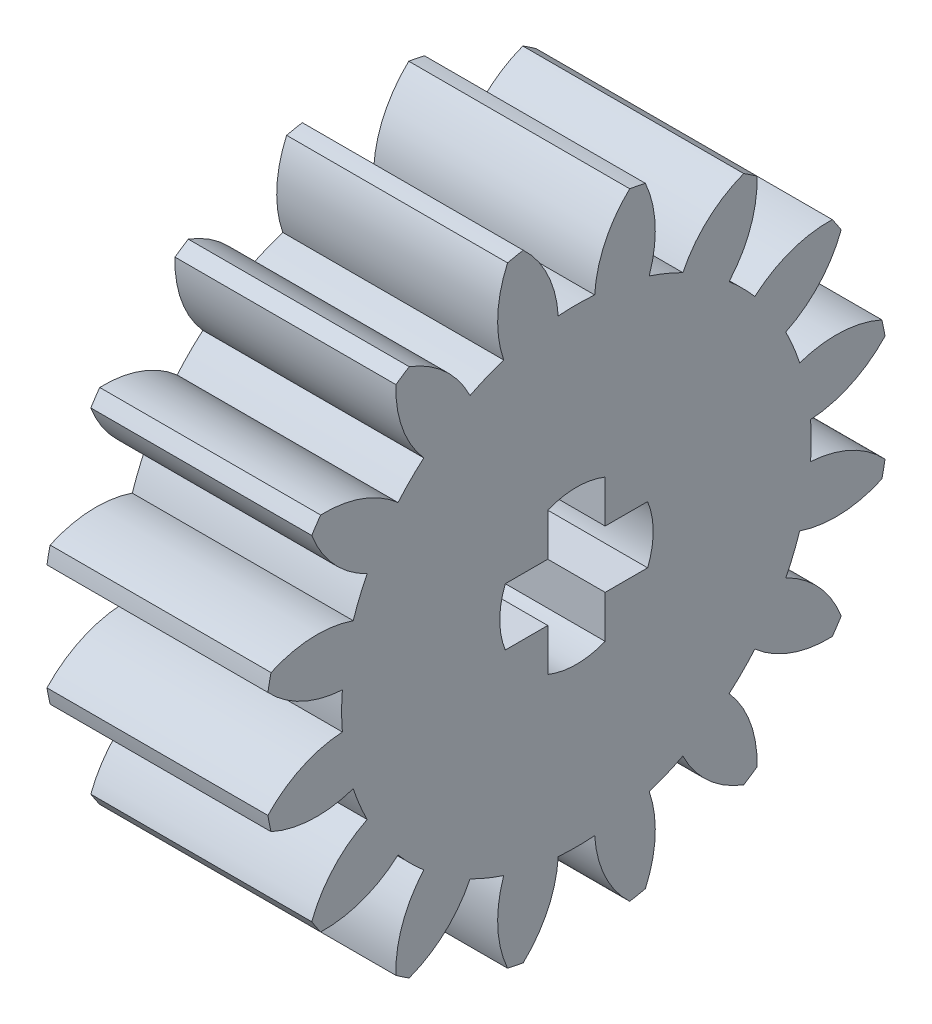
SolidWorks part; units mm, degrees
ref_plane "Plane1" through (0, 0, 0) normal (0, 0, 1) x (1, 0, 0)
ref_plane "Plane2" through (0, 0, 0) normal (0, 1, 0) x (1, 0, 0)
ref_plane "Plane3" through (0, 0, 0) normal (1, 0, 0) x (0, 0, -1)
sketch "HoldingSke" plane through (0, 0, 0) normal (0, 1, 0) x (1, 0, 0)
  line L0 (0, 0) -> (0.9613, -0.2756)
  line L1 (-15, 0) -> (100, 0) construction
  line L2 (0, 0) -> (-2.1039, 2.3779)
  line L3 (0, 0) -> (-11.863, 4.5341)
  line L4 (0, 0) -> (8.3015, 2.3804)
  line L5 (0, 0) -> (-46.8476, -17.4728)
  line L6 (0, 0) -> (-5.2639, -3.5516)
  line L7 (-2.1039, 2.3779) -> (8.6586, 51.2059)
  line L8 (-76.2, 54.61) -> (-76.1, 54.61)
  line L9 (-71.009, 38.7566) -> (-53.1078, 45.2721)
  line L10 (-76.2, 71.12) -> (104.1128, 71.12)
  line L11 (0, 0) -> (-6.35, 0)
  line L12 (-76.2, 101.6) -> (-76.162, 101.6)
  line L13 (24.9733, 27.94) -> (52.9518, 28.4284)
  line L14 (24.9733, 27.94) -> (24.9743, 27.94)
  line L15 (24.9733, 27.94) -> (100.4006, 29.5858)
  line L16 (-63.627, -1) -> (-12.827, -1)
  circle A0 centre (0, 0) radius 0.5
  circle A1 centre (0, 0) radius 6.749
  circle A2 centre (0, 0) radius 37.5
  circle A3 centre (0, 0) radius 0.5
  dimension "MHD" = 13.498
  dimension "Hub_dia" = 75
  dimension "Bore" = 1
  dimension "MBD" = 1
  dimension "Num_teeth" = 16
  dimension "Pitch_radius" = 180.3128
  dimension "Pitch" = 1
  dimension "Width" = 6.35
  dimension "Overall_len" = 50
  dimension "Show_teeth" = 16
  dimension "Thickness" = 6.35
  dimension "OAL" = 50.0001
  dimension "T_dim" = 0.1
  dimension "Ap" = 20
  dimension "H" = 19.05
  dimension "Backlash" = 0.038
  dimension "Addendum_fac" = 1
  dimension "Dedendum_fac" = 1.25
  dimension "Clearance_fac" = 0.25
  dimension "Dedendum_add" = 0.001
  dimension "Module" = 1
sketch "BasProSke" plane through (0, 0, 0) normal (0, 1, 0) x (1, 0, 0)
  line L0 (-10, 0) -> (60, 0) construction
  line L1 (0, 0) -> (0, 9)
  line L2 (0, 0) -> (6.35, 0)
  line L3 (6.35, 0) -> (6.35, 9)
  line L4 (6.35, 9) -> (0, 9)
  dimension "Diameter" = 18
  dimension "Thickness" = 6.35
revolve "Base-Revolve" add sketch "BasProSke" angle 360 about L0
sketch "TooCutSke" plane through (0, 0, 0) normal (1, 0, 0) x (0, 0, -1)
  line L1 (0, 0) -> (0, 107) construction
  line L2 (0, 0) -> (-0.8506, 7.9547) construction
  line L3 (0, 0) -> (-3.1089, 15.6293) construction
  line L4 (-0.8506, 7.9547) -> (-1.5544, 7.8146) construction
  arc A0 (0.5238, 6.7286) -> (-0.5238, 6.7286) centre (0, 0) ccw
  arc A1 (1.5534, 8.8907) -> (-1.5534, 8.8907) centre (0, 0) ccw
  circle A2 centre (0, 0) radius 8 construction
  circle A3 centre (0, 0) radius 7.5175 construction
  arc A4 (-0.5238, 6.7286) -> (-1.5534, 8.8907) centre (-3.7179, 6.5338) ccw
  arc A5 (1.5534, 8.8907) -> (0.5238, 6.7286) centre (3.7179, 6.5338) ccw
  dimension "Root_dia" = 13.498
  dimension "Overcut_dia" = 18.0508
  dimension "Pitch_dia" = 16
  dimension "Base_dia" = 15.0351
  dimension "Flank_rad" = 3.2
  dimension "Half_ang" = 11.25
  dimension "Half_CT" = 0.7176
extrude "ToothCut" cut sketch "TooCutSke" along normal through all
fillet "Breaks" [suppressed] radius 0.02
fillet "RootFillets" [suppressed] radius 0.251
pattern_circular "TeethCuts" count 16 every 22.5 about axis through (-10, 0, 0) along (1, 0, 0) of "ToothCut", "RootFillets", "Breaks"
sketch "HubNeaOneSke" plane through (0, 0, 0) normal (-1, 0, 0) x (0, 0, 1)
  circle A0 centre (0, 0) radius 6.749
  dimension "Diameter" = 13.498
extrude "HubNearOne" [suppressed] add sketch "HubNeaOneSke" along normal blind 43.6501
sketch "HubNeaBotSke" plane through (0, 0, 0) normal (-1, 0, 0) x (0, 0, 1)
  circle A0 centre (0, 0) radius 6.749
  dimension "Diameter" = 13.498
extrude "HubNearBoth" [suppressed] add sketch "HubNeaBotSke" along normal blind 21.825
ref_plane "FarPln" through (6.35, 0, 0) normal (1, 0, 0) x (0, 0, -1)
sketch "HubFarSke" plane through (6.35, 0, 0) normal (1, 0, 0) x (0, 0, -1)
  circle A0 centre (0, 0) radius 6.749
  dimension "Diameter" = 13.498
extrude "HubFar" [suppressed] add sketch "HubFarSke" along normal blind 21.825
sketch "BorSke" plane through (0, 0, 0) normal (1, 0, 0) x (0, 0, -1)
  circle A0 centre (0, 0) radius 0.5
  dimension "Diameter" = 1
extrude "Bore" cut sketch "BorSke" along normal mid plane 100.0001
sketch "KeySke" plane through (0, 0, 0) normal (1, 0, 0) x (0, 0, -1)
  line L0 (-0.05, 0) -> (-0.05, 0.6)
  line L1 (-0.05, 0.6) -> (0.05, 0.6)
  line L2 (0.05, 0.6) -> (0.05, 0)
  line L3 (0, 0) -> (0, 34) construction
  line L4 (-0.05, 0) -> (0.05, 0)
  dimension "Offset" = 0.6
  dimension "Width" = 0.1
extrude "Keyway" [suppressed] cut sketch "KeySke" along normal mid plane 100.0001
pattern_circular "Keyway2" [suppressed] count 2 every 90 about axis through (-10, 0, 0) along (1, 0, 0)
sketch "Sketch1" plane through (6.35, 0, 0) normal (1, 0, 0) x (0, 0, -1)
  line L0 (-0.8249, 2.0449) -> (-0.8249, 0.8249)
  line L1 (-0.8249, 0.8249) -> (-2.0449, 0.8249)
  line L2 (-2.0449, -0.8249) -> (-0.8249, -0.8249)
  line L3 (-0.8249, -0.8249) -> (-0.8249, -2.0449)
  line L4 (0.8249, -2.0449) -> (0.8249, -0.8249)
  line L5 (0.8249, -0.8249) -> (2.0449, -0.8249)
  line L6 (2.0449, 0.8249) -> (0.8249, 0.8249)
  line L7 (0.8249, 0.8249) -> (0.8249, 2.0449)
  circle A0 centre (0, 0) radius 2.205
  dimension "D1" = 4.41
  dimension "D2" = 1.22
extrude "Cut-Extrude1" cut sketch "Sketch1" against normal blind 10 contours L7 A0 L0 L1 L2 L3 L4 L5 L6
equation "' \"Module@HoldingSke\" = 6.35"
equation "' \"Num_teeth@HoldingSke\" = 12"
equation "' \"Ap@HoldingSke\" =  20"
equation "' \"Width@HoldingSke\" = 0.5 * 25.4"
equation "' \"Hub_dia@HoldingSke\"= 1 * 25.4"
equation "' \"Overall_len@HoldingSke\" = 1.0 * 25.4"
equation "' \"Bore@HoldingSke\" = 0.75 * 25.4"
equation "' \"T_dim@HoldingSke\" = 0.1 * 25.4"
equation "' \"Width@KeySke\" = 0.25 * 25.4"
equation "' \"Show_teeth@HoldingSke\" = 13"
equation "' \"Backlash@HoldingSke\" = 0.009 * 25.4"
equation "' \"Addendum_fac@HoldingSke\" = 1.0"
equation "' \"Dedendum_fac@HoldingSke\" = 1.25"
equation "' \"Dedendum_add@HoldingSke\" = 0.00005 * 25.4"
equation "' \"Clearance_fac@HoldingSke\" = 0.25"
equation "\"Pitch@HoldingSke\" = 1 / \"Module@HoldingSke\""
equation "\"Overcut_dia@TooCutSke\" = (\"Num_teeth@HoldingSke\" + 2 * \"Addendum_fac@HoldingSke\") / \"Pitch@HoldingSke\" + 0.002 * 25.4"
equation "\"Pitch_dia@TooCutSke\" = \"Num_teeth@HoldingSke\" / \"Pitch@HoldingSke\""
equation "\"Base_dia@TooCutSke\" = \"Num_teeth@HoldingSke\" / \"Pitch@HoldingSke\" * cos((\"Ap@HoldingSke\"  * 3.14159265 / 180))"
equation "\"Root_dia@TooCutSke\" = (\"Num_teeth@HoldingSke\" + 2) / \"Pitch@HoldingSke\" - 2 * (\"Addendum_fac@HoldingSke\" + \"Dedendum_fac@HoldingSke\") / \"Pitch@HoldingSke\" - \"Dedendum_add@HoldingSke\" * 2"
equation "\"Half_ang@TooCutSke\" = 180 / \"Num_teeth@HoldingSke\""
equation "\"Half_CT@TooCutSke\" = \"Num_teeth@HoldingSke\" / \"Pitch@HoldingSke\" * sin((3.14159265 / 2 / \"Num_teeth@HoldingSke\")) / 2 - 7 * \"Backlash@HoldingSke\" / 4"
equation "\"Flank_rad@TooCutSke\" = \"Num_teeth@HoldingSke\" / \"Pitch@HoldingSke\" / 5"
equation "\"Radius@RootFillets\" = \"Clearance_fac@HoldingSke\" / \"Pitch@HoldingSke\" + \"Dedendum_add@HoldingSke\""
equation "\"Break_rad@Breaks\" = 0.02 / \"Pitch@HoldingSke\""
equation "\"Thickness@HoldingSke\" = \"Width@HoldingSke\""
equation "\"OAL@HoldingSke\" = \"Thickness@HoldingSke\""
equation "\"MHD@HoldingSke\" = (\"Num_teeth@HoldingSke\" + 2) / \"Pitch@HoldingSke\" - 2 * (\"Addendum_fac@HoldingSke\" + \"Dedendum_fac@HoldingSke\")  / \"Pitch@HoldingSke\" - \"Dedendum_add@HoldingSke\" * 2"
equation "\"MBD@HoldingSke\" = (\"Num_teeth@HoldingSke\" + 2) / \"Pitch@HoldingSke\" - 2 * (\"Addendum_fac@HoldingSke\" + \"Dedendum_fac@HoldingSke\")  / \"Pitch@HoldingSke\" - \"Dedendum_add@HoldingSke\" * 2 - 0.002 * 25.4"
equation "\"MHD@HoldingSke\" = ((sgn( \"MHD@HoldingSke\" - \"Hub_dia@HoldingSke\" )-1)*( \"MHD@HoldingSke\" - \"Hub_dia@HoldingSke\" ))/-2+ \"Hub_dia@HoldingSke\""
equation "\"MBD@HoldingSke\" = ((sgn( \"MBD@HoldingSke\" - \"Bore@HoldingSke\" )-1)*( \"MBD@HoldingSke\" - \"Bore@HoldingSke\" ))/-2+ \"Bore@HoldingSke\""
equation "\"OAL@HoldingSke\" = ((sgn( \"OAL@HoldingSke\" - \"Overall_len@HoldingSke\" )+1)*( \"OAL@HoldingSke\" - \"Overall_len@HoldingSke\" ))/2 + \"Overall_len@HoldingSke\" + 0.000002 * 25.4"
equation "\"Num_teeth@TeethCuts\" = int( \"Show_teeth@HoldingSke\" ) + 1"
equation "\"Num_teeth@TeethCuts\" = ((sgn( \"Num_teeth@TeethCuts\" - \"Num_teeth@HoldingSke\" )-1)*( \"Num_teeth@TeethCuts\" - \"Num_teeth@HoldingSke\" ))/-2+ \"Num_teeth@HoldingSke\""
equation "\"Num_teeth@TeethCuts\" = ((sgn( \"Num_teeth@TeethCuts\" - 2.0)+1)*( \"Num_teeth@TeethCuts\" - 2.0))/2 +2.0"
equation "\"Angle@TeethCuts\" = 360.0 / \"Num_teeth@HoldingSke\""
equation "\"Diameter@BasProSke\" = (\"Num_teeth@HoldingSke\" + 2 * \"Addendum_fac@HoldingSke\") / \"Pitch@HoldingSke\""
equation "\"Thickness@BasProSke\"  = \"Thickness@HoldingSke\""
equation "' \"Fillet_rad@BasProSke\" =  \"Thickness@HoldingSke\" * 0.05"
equation "\"MHD@HoldingSke\" = ((sgn( \"MHD@HoldingSke\" - \"Root_dia@TooCutSke\" )-1)*( \"MHD@HoldingSke\" - \"Root_dia@TooCutSke\" ))/-2+ \"Root_dia@TooCutSke\""
equation "\"Diameter@HubNeaOneSke\" = \"MHD@HoldingSke\""
equation "\"Length@HubNearOne\" = \"OAL@HoldingSke\" - \"Thickness@BasProSke\""
equation "\"Diameter@HubNeaBotSke\" = \"MHD@HoldingSke\""
equation "\"Length@HubNearBoth\" = ( \"OAL@HoldingSke\" - \"Thickness@BasProSke\" ) / 2.0"
equation "\"Thickness@FarPln\" = \"Thickness@BasProSke\""
equation "\"Diameter@HubFarSke\" = \"MHD@HoldingSke\""
equation "\"Length@HubFar\" = ( \"OAL@HoldingSke\" - \"Thickness@BasProSke\" ) / 2.0"
equation "\"Diameter@BorSke\" = \"MBD@HoldingSke\""
equation "\"D1@Bore\" = \"OAL@HoldingSke\" * 2.0"
equation "\"D1@Keyway\" = \"OAL@HoldingSke\" * 2.0"
equation "\"Offset@KeySke\" = \"T_dim@HoldingSke\" + \"MBD@HoldingSke\" / 2.0"
